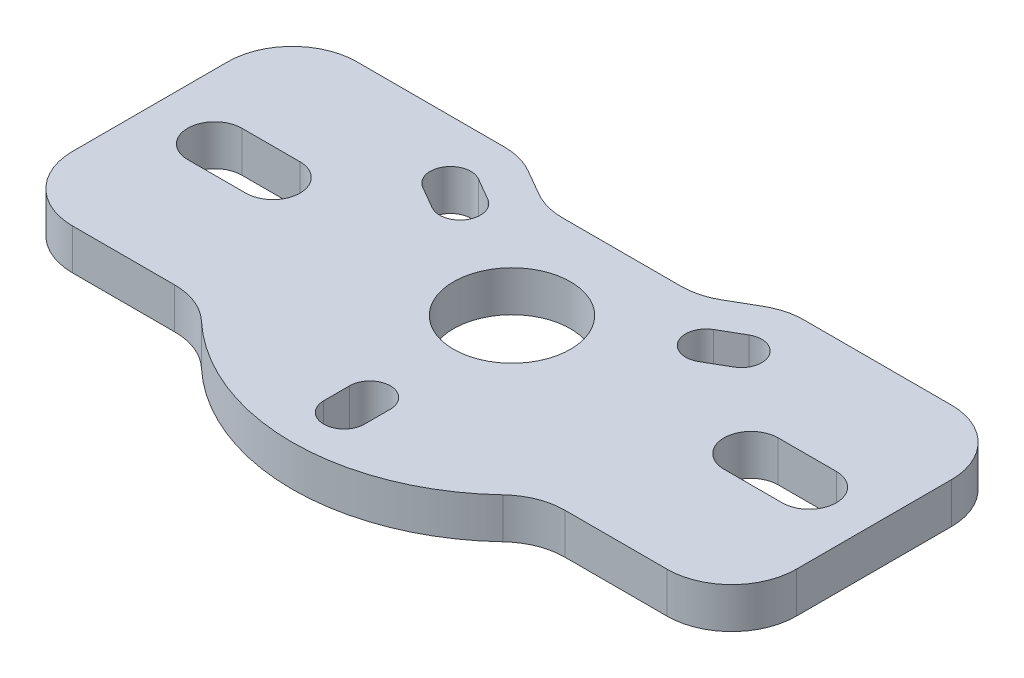
SolidWorks part; units mm, degrees
material "CA"
ref_plane "Front Plane" through (0, 0, 0) normal (0, 0, 1) x (1, 0, 0)
ref_plane "Top Plane" through (0, 0, 0) normal (0, 1, 0) x (1, 0, 0)
ref_plane "Right Plane" through (0, 0, 0) normal (1, 0, 0) x (0, 0, -1)
sketch "Sketch1" plane through (0, 0, 0) normal (0, 1, 0) x (1, 0, 0)
  line L0 (14.7222, 13.97) -> (29.21, 13.97)
  line L1 (-29.21, 13.97) -> (-14.7222, 13.97)
  line L2 (-35.56, 7.62) -> (-35.56, -7.62)
  line L3 (-11.5472, 13.1193) -> (-8.995, 11.6457)
  line L4 (35.56, 7.62) -> (35.56, -7.62)
  line L5 (-23.495, 0) -> (-29.21, 0) construction
  line L6 (-23.495, -2.667) -> (-29.21, -2.667)
  line L7 (-23.495, 2.667) -> (-29.21, 2.667)
  line L8 (23.495, 0) -> (29.21, 0) construction
  line L9 (23.495, 2.667) -> (29.21, 2.667)
  line L10 (23.495, -2.667) -> (29.21, -2.667)
  line L11 (-14.2894, 8.25) -> (0, 0) construction
  line L12 (0, 0) -> (14.2894, 8.25) construction
  line L13 (-15.2894, 6.5179) -> (-13.0897, 5.2479)
  line L14 (-13.2894, 9.9821) -> (-11.0897, 8.7121)
  line L15 (13.2894, 9.9821) -> (11.0897, 8.7121)
  line L16 (15.2894, 6.5179) -> (13.0897, 5.2479)
  line L17 (2, -16.5) -> (2, -13.96)
  line L18 (-2, -13.96) -> (-2, -16.5)
  line L19 (-29.21, -13.97) -> (-19.1766, -13.97)
  line L20 (19.1766, -13.97) -> (29.21, -13.97)
  line L21 (-5.82, 10.795) -> (5.82, 10.795)
  line L22 (8.995, 11.6457) -> (11.5472, 13.1193)
  circle A0 centre (0, 0) radius 5.75
  arc A1 (-23.495, -2.667) -> (-23.495, 2.667) centre (-23.495, 0) ccw
  arc A2 (-29.21, 2.667) -> (-29.21, -2.667) centre (-29.21, 0) ccw
  arc A3 (23.495, 2.667) -> (23.495, -2.667) centre (23.495, 0) ccw
  arc A4 (29.21, -2.667) -> (29.21, 2.667) centre (29.21, 0) ccw
  arc A5 (-13.2894, 9.9821) -> (-15.2894, 6.5179) centre (-14.2894, 8.25) ccw
  arc A6 (15.2894, 6.5179) -> (13.2894, 9.9821) centre (14.2894, 8.25) ccw
  circle A7 centre (0, 0) radius 20 construction
  arc A8 (29.21, 13.97) -> (35.56, 7.62) centre (29.21, 7.62) cw
  arc A9 (29.21, -13.97) -> (35.56, -7.62) centre (29.21, -7.62) ccw
  arc A10 (19.1766, -13.97) -> (14.8183, -15.7018) centre (19.1766, -20.32) ccw
  arc A11 (-29.21, 13.97) -> (-35.56, 7.62) centre (-29.21, 7.62) ccw
  circle A12 centre (0, 0) radius 16.5 construction
  arc A13 (-2, -16.5) -> (2, -16.5) centre (0, -16.5) ccw
  arc A14 (5.82, 10.795) -> (8.995, 11.6457) centre (5.82, 17.145) ccw
  arc A15 (11.5472, 13.1193) -> (14.7222, 13.97) centre (14.7222, 7.62) cw
  arc A16 (-14.7222, 13.97) -> (-11.5472, 13.1193) centre (-14.7222, 7.62) cw
  arc A17 (-13.0897, 5.2479) -> (-11.0897, 8.7121) centre (-12.0897, 6.98) ccw
  arc A18 (11.0897, 8.7121) -> (13.0897, 5.2479) centre (12.0897, 6.98) ccw
  arc A19 (2, -13.96) -> (-2, -13.96) centre (0, -13.96) ccw
  arc A20 (-14.8183, -15.7018) -> (14.8183, -15.7018) centre (0, 0) ccw
  arc A21 (-19.1766, -13.97) -> (-14.8183, -15.7018) centre (-19.1766, -20.32) cw
  arc A22 (-29.21, -13.97) -> (-35.56, -7.62) centre (-29.21, -7.62) cw
  arc A23 (-8.995, 11.6457) -> (-5.82, 10.795) centre (-5.82, 17.145) ccw
  point P9 (-26.3525, 0)
  point P14 (26.3525, 0)
  point P42 (11.6397, 13.97)
  point P50 (-16.4611, -13.97)
  dimension "D3" = 11.5
  dimension "D10" = 40
  dimension "D11" = 6.35
  dimension "D8" = 33
  dimension "D9" = 4
  dimension "D13" = 10.795
  dimension "D18" = 6.35
  dimension "D16" = 21.59
  dimension "D21" = 6.35
  dimension "D14" = 6.35
  dimension "D2" = 71.12
  dimension "D4" = 23.495
  dimension "D5" = 23.495
  dimension "D6" = 29.21
  dimension "D7" = 5.334
  dimension "D12" = 120
  dimension "D15" = 13.97
  dimension "D17" = 35.56
  dimension "D19" = 2.54
  dimension "D20" = 13.97
  dimension "D22" = 5.588
  dimension "D23" = 5.588
extrude "Boss-Extrude1" add sketch "Sketch1" along normal blind 4
sketch "Sketch5" plane through (0, 4, 0) normal (0, 1, 0) x (1, 0, 0)
  line L0 (-3.9688, -13.96) -> (-3.9688, -16.5)
  line L1 (3.9688, -16.5) -> (3.9688, -13.96)
  line L2 (12.305, 11.687) -> (10.1053, 10.417)
  line L3 (16.2738, 4.813) -> (14.0741, 3.543)
  line L4 (-12.305, 11.687) -> (-10.1053, 10.417)
  line L5 (-16.2738, 4.813) -> (-14.0741, 3.543)
  arc A0 (16.2738, 4.813) -> (12.305, 11.687) centre (14.2894, 8.25) ccw
  arc A1 (-12.305, 11.687) -> (-16.2738, 4.813) centre (-14.2894, 8.25) ccw
  arc A2 (-3.9688, -16.5) -> (3.9688, -16.5) centre (0, -16.5) ccw
  arc A3 (-14.0741, 3.543) -> (-10.1053, 10.417) centre (-12.0897, 6.98) ccw
  arc A4 (3.9688, -13.96) -> (-3.9688, -13.96) centre (0, -13.96) ccw
  arc A5 (10.1053, 10.417) -> (14.0741, 3.543) centre (12.0897, 6.98) ccw
  dimension "D1" = 7.9375
ref_plane "Plane1" through (0, 0, 0) normal (0.5, 0, 0.866) x (0.866, 0, -0.5)
